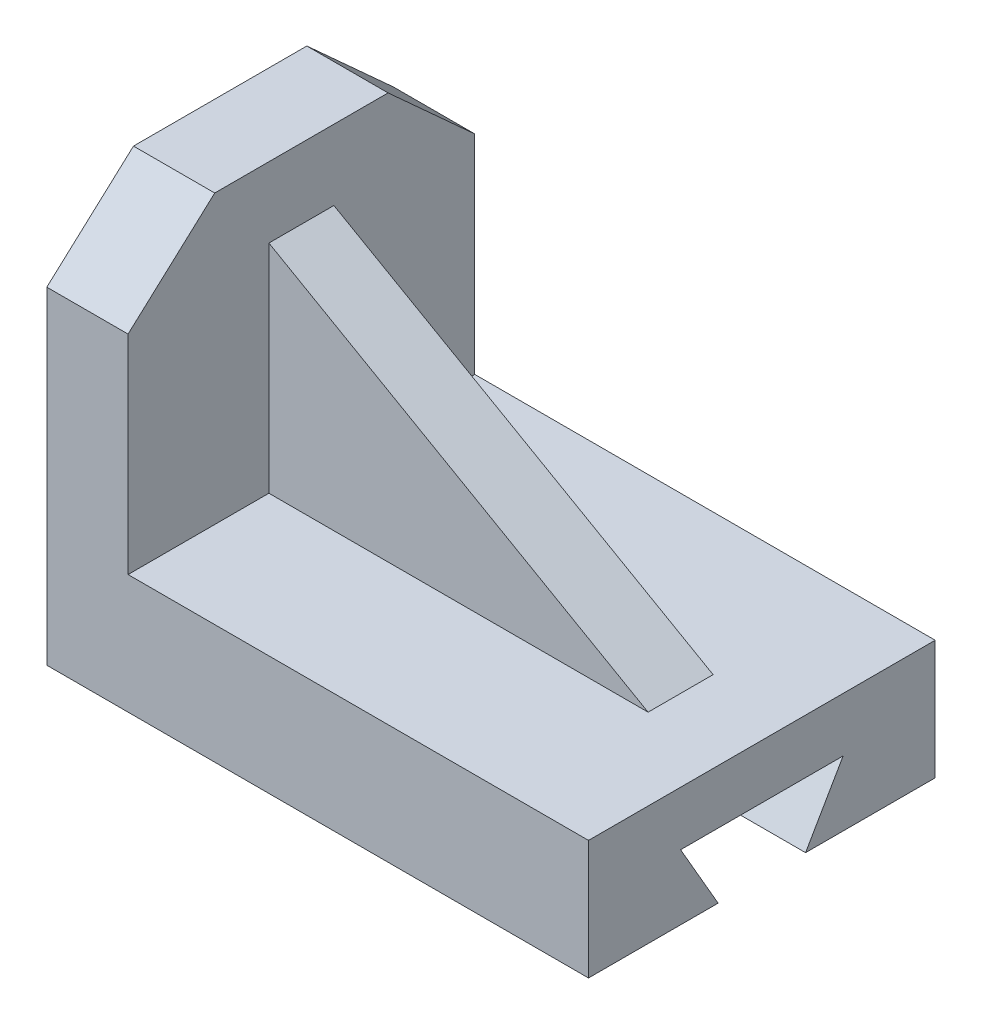
SolidWorks part; units mm, degrees
ref_plane "Front Plane" through (0, 0, 0) normal (0, 0, 1) x (1, 0, 0)
ref_plane "Top Plane" through (0, 0, 0) normal (0, 1, 0) x (1, 0, 0)
ref_plane "Right Plane" through (0, 0, 0) normal (1, 0, 0) x (0, 0, -1)
sketch "Sketch1" plane through (0, 0, 0) normal (0, 0, 1) x (1, 0, 0)
  line L1 (-28.1469, -35.5013) -> (71.8531, -35.5013)
  line L2 (71.8531, -35.5013) -> (71.8531, -13.5013)
  line L3 (71.8531, -13.5013) -> (56.8531, -13.5013)
  line L4 (-13.1469, 39.4987) -> (-13.1469, 26.4987)
  line L7 (-13.1469, 39.4987) -> (-13.1469, 26.4987)
  line L8 (56.8531, -13.5013) -> (-13.1469, -13.5013)
  line L9 (-13.1469, 26.4987) -> (56.8531, -13.5013)
  line L10 (-28.1469, 39.4987) -> (-28.1469, -35.5013)
  line L11 (-13.1469, 39.4987) -> (-28.1469, 39.4987)
  line L12 (-13.1469, 26.4987) -> (-13.1469, -13.5013)
  dimension "D1" = 75
  dimension "D2" = 100
  dimension "D3" = 15
  dimension "D4" = 40
  dimension "D5" = 15
  dimension "D7" = 22
extrude "Boss-Extrude2" add sketch "Sketch1" along normal mid plane 64 contours L9 L12 L8 | L12 L4 L11 L10 L1 L2 L3 L8
sketch "Sketch3" plane through (0, 0, 32) normal (0, 0, 1) x (1, 0, 0)
  line L0 (-13.1469, 26.4987) -> (-13.1469, -13.5013)
  line L1 (56.8531, -13.5013) -> (-13.1469, -13.5013)
  line L2 (-13.1469, 26.4987) -> (56.8531, -13.5013)
extrude "Cut-Extrude2" cut sketch "Sketch3" against normal blind 21
sketch "Sketch4" plane through (0, 0, -32) normal (0, 0, -1) x (-1, 0, 0)
  line L0 (13.1469, 26.4987) -> (13.1469, -13.5013)
  line L1 (-56.8531, -13.5013) -> (13.1469, -13.5013)
  line L2 (-56.8531, -13.5013) -> (13.1469, 26.4987)
extrude "Cut-Extrude3" cut sketch "Sketch4" against normal blind 21
sketch "Sketch8" plane through (0, 0, 11) normal (0, 0, 1) x (1, 0, 0)
  line L0 (-13.1469, 26.4987) -> (56.8531, -13.5013)
  line L1 (56.8531, -13.5013) -> (-13.1469, -13.5013)
  line L2 (-13.1469, -13.5013) -> (-13.1469, 26.4987)
extrude "Cut-Extrude4" cut sketch "Sketch8" against normal blind 5
sketch "Sketch9" plane through (0, 0, -11) normal (0, 0, -1) x (-1, 0, 0)
  line L0 (13.1469, 26.4987) -> (-56.8531, -13.5013)
  line L1 (-56.8531, -13.5013) -> (13.1469, -13.5013)
  line L2 (13.1469, -13.5013) -> (13.1469, 26.4987)
extrude "Cut-Extrude5" cut sketch "Sketch9" against normal blind 5
sketch "Sketch10" plane through (-13.1469, 0, 0) normal (1, 0, 0) x (0, 0, -1)
  line L0 (-32, 39.4987) -> (-16, 39.4987)
  line L1 (-32, 39.4987) -> (32, 39.4987) construction
  line L2 (-16, 39.4987) -> (-32, 24.9465)
  line L3 (-32, 39.4987) -> (-32, -13.5013) construction
  line L4 (-32, 24.9465) -> (-32, 40.9465)
  line L7 (32, 39.4987) -> (16, 39.4987)
  line L8 (16, 39.4987) -> (32, 24.9465)
  line L9 (32, 24.9465) -> (32, 40.9465)
  line M9 (32, -13.5013) -> (32, 39.4987)
  line M10 (32, 39.4987) -> (-32, 39.4987)
  line M11 (-32, 39.4987) -> (-32, -13.5013)
  dimension "D1" = 16
  dimension "D2" = 16
extrude "Cut-Extrude6" cut sketch "Sketch10" against normal up to next contours L2 M10 M11 | L8 M10 M9
sketch "Sketch11" plane through (71.8531, 0, 0) normal (1, 0, 0) x (0, 0, -1)
  line L2 (-8.0718, -35.5013) -> (8.0718, -35.5013)
  line L3 (-32, -35.5013) -> (32, -35.5013) construction
  line L4 (8.0718, -35.5013) -> (15, -23.5013)
  line L5 (15, -23.5013) -> (-15, -23.5013)
  line L8 (-8.0718, -35.5013) -> (-15, -23.5013)
extrude "Cut-Extrude7" cut sketch "Sketch11" against normal up to next
